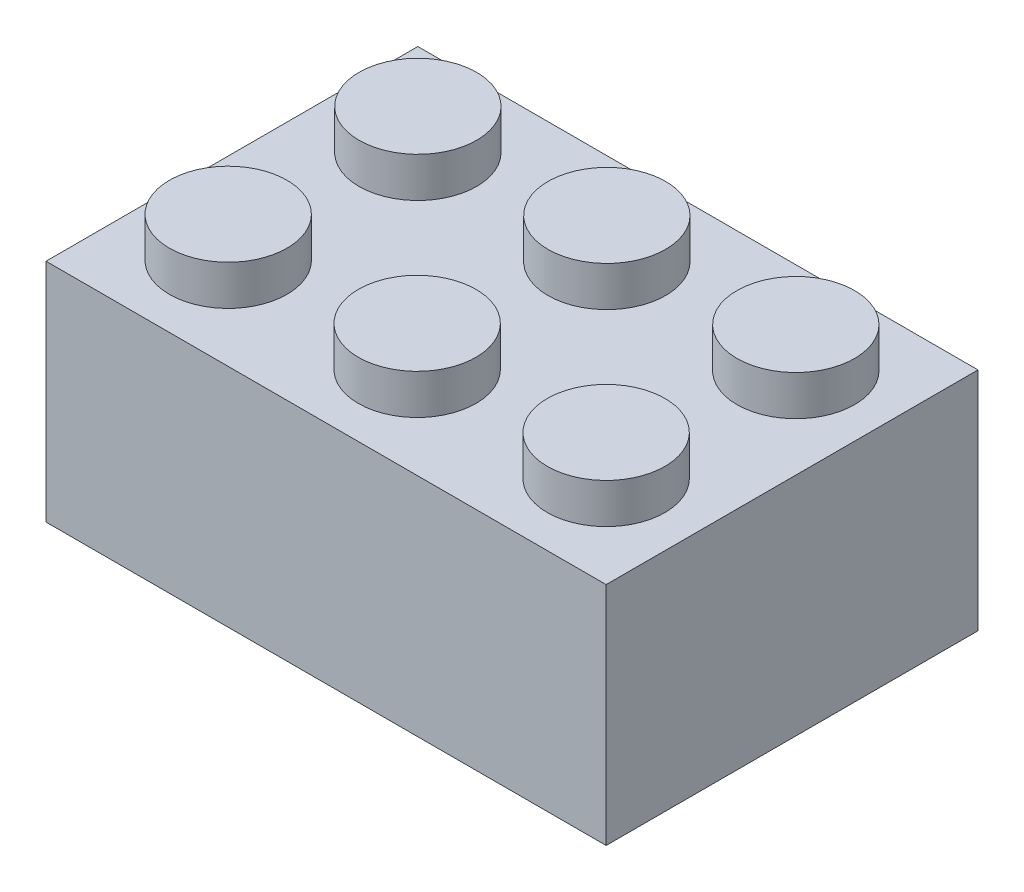
SolidWorks part; units mm, degrees
ref_plane "Спереди" through (0, 0, 0) normal (0, 0, 1) x (1, 0, 0)
ref_plane "Сверху" through (0, 0, 0) normal (0, 1, 0) x (1, 0, 0)
ref_plane "Справа" through (0, 0, 0) normal (1, 0, 0) x (0, 0, -1)
sketch "Эскиз5" plane through (0, 0, 0) normal (0, 1, 0) x (1, 0, 0)
  line L1 (0, 0) -> (23.8, 0)
  line L2 (0, 0) -> (0, 15.8)
  line L3 (0, 15.8) -> (23.8, 15.8)
  line L4 (23.8, 0) -> (23.8, 15.8)
  dimension "D1" = 23.8
  dimension "D2" = 15.8
extrude "Бобышка-Вытянуть2" add sketch "Эскиз5" along normal blind 9.6 contours L2 L1 L4 L3
sketch "Эскиз6" plane through (0, 9.6, 0) normal (0, 1, 0) x (1, 0, 0)
  line L0 (0, 15.8) -> (23.8, 15.8) construction
  line L1 (0, 0) -> (0, 15.8) construction
  line L2 (23.8, 0) -> (23.8, 15.8) construction
  line L3 (0, 0) -> (23.8, 0) construction
  circle A0 centre (3.9, 11.9) radius 2.5
  circle A1 centre (11.9291, 11.9) radius 2.5
  circle A2 centre (19.9583, 11.9) radius 2.5
  circle A3 centre (11.8709, 3.9) radius 2.5
  circle A4 centre (19.9, 3.9) radius 2.5
  circle A5 centre (3.8417, 3.9) radius 2.5
  dimension "D1" = 5
  dimension "D4" = 3
  dimension "D2" = 3.9
  dimension "D3" = 3.9
  dimension "D6" = 3.9
  dimension "D7" = 3.9
  dimension "D5" = 2
extrude "Бобышка-Вытянуть3" add sketch "Эскиз6" along normal blind 1.7
sketch "Эскиз7" plane through (0, 0, 0) normal (0, -1, 0) x (1, 0, 0)
  line L0 (0, 0) -> (0, -15.8) construction
  line L1 (0, 0) -> (23.8, 0) construction
  line L2 (23.8, 0) -> (23.8, -15.8) construction
  line L3 (0, -15.8) -> (23.8, -15.8) construction
  circle A0 centre (3.9, -3.9) radius 2.6
  circle A1 centre (11.9, -3.9) radius 2.6
  circle A2 centre (19.9, -3.9) radius 2.6
  circle A3 centre (11.9, -11.9) radius 2.6
  circle A4 centre (19.9, -11.9) radius 2.6
  circle A5 centre (3.9, -11.9) radius 2.6
  dimension "D1" = 5.2
  dimension "D2" = 3.9
  dimension "D3" = 3.9
  dimension "D6" = 3.9
  dimension "D7" = 3.9
  dimension "D4" = 3
  dimension "D5" = 2
extrude "Вырез-Вытянуть1" cut sketch "Эскиз7" against normal blind 1.8
